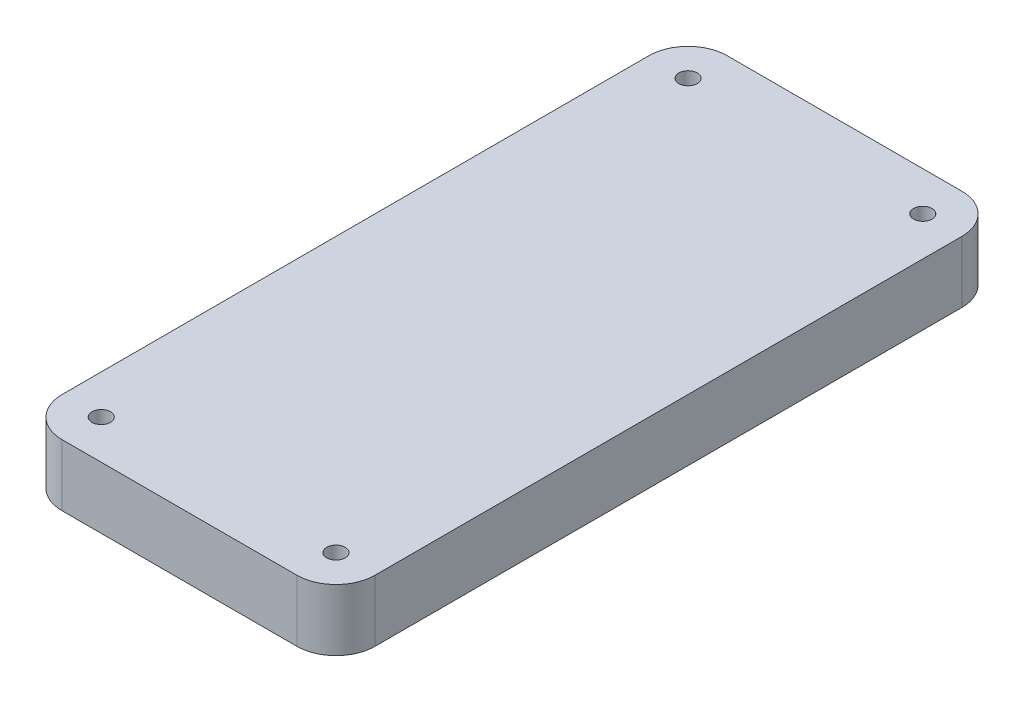
SolidWorks part; units mm, degrees
ref_plane "Front Plane" through (0, 0, 0) normal (0, 0, 1) x (1, 0, 0)
ref_plane "Top Plane" through (0, 0, 0) normal (0, 1, 0) x (1, 0, 0)
ref_plane "Right Plane" through (0, 0, 0) normal (1, 0, 0) x (0, 0, -1)
sketch "Sketch1" plane through (0, 0, 0) normal (0, 1, 0) x (1, 0, 0)
  line L1 (0, 0) -> (101.6, 0)
  line L2 (0, 0) -> (0, 215.9)
  line L3 (0, 215.9) -> (101.6, 215.9)
  line L4 (101.6, 0) -> (101.6, 215.9)
  dimension "9" = 215.9
  dimension "5.5" = 101.6
extrude "Boss-Extrude2" add sketch "Sketch1" along normal blind 20
sketch "Sketch4" plane through (0, 20, -20) normal (0, -1, 0) x (1, 0, 0)
  line L0 (101.6, -277.6562) -> (-114.3, -277.6563) construction
  line L1 (101.6, -246.7) -> (-114.3, -246.7) construction
  line L2 (101.6, -297.5) -> (-114.3, -297.5)
  line L3 (101.6, -297.5) -> (101.6, -195.9)
  line L4 (101.6, -195.9) -> (-114.3, -195.9)
  line L5 (-114.3, -297.5) -> (-114.3, -195.9)
  line L7 (0, 20) -> (101.6, 20) construction
  line L9 (0, -195.9) -> (0, 20) construction
  circle A0 centre (70.6438, -277.6562) radius 3.1
  circle A1 centre (-108.7437, -277.6563) radius 3.1
  circle A2 centre (70.6437, -215.7437) radius 3.1
  circle A3 centre (-108.7437, -215.7437) radius 3.1
  dimension "D2" = 6.2
  dimension "D3" = 30.9562
  dimension "D1" = 30.9562
  dimension "D4" = 2
fillet "Fillet1" radius 12.7 4 edges at (0, 10, -215.9) (101.6, 10, -215.9) (0, 10, 0) (101.6, 10, 0)
sketch "Sketch5" plane through (0, 0, 0) normal (0, -1, 0) x (-1, 0, 0)
  line L0 (-88.9, 215.9) -> (-12.7, 215.9) construction
  line L1 (-101.6, 12.7) -> (-101.6, 203.2) construction
  circle A0 centre (-88.9, 203.2) radius 3
  circle A1 centre (-12.7, 203.2) radius 3
  circle A2 centre (-88.9, 12.7) radius 3
  circle A3 centre (-12.7, 12.7) radius 3
  point P8 (0, 0)
  dimension "D1" = 6
  dimension "D2" = 12.7
  dimension "D3" = 12.7
  dimension "D4" = 76.2
  dimension "D5" = 190.5
  dimension "D6" = 190.5
  dimension "D7" = 12.7
  dimension "D8" = 76.2
  dimension "D9" = 12.7
extrude "Cut-Extrude1" cut sketch "Sketch5" against normal through all
equation "\"2c\"=0.787402"
